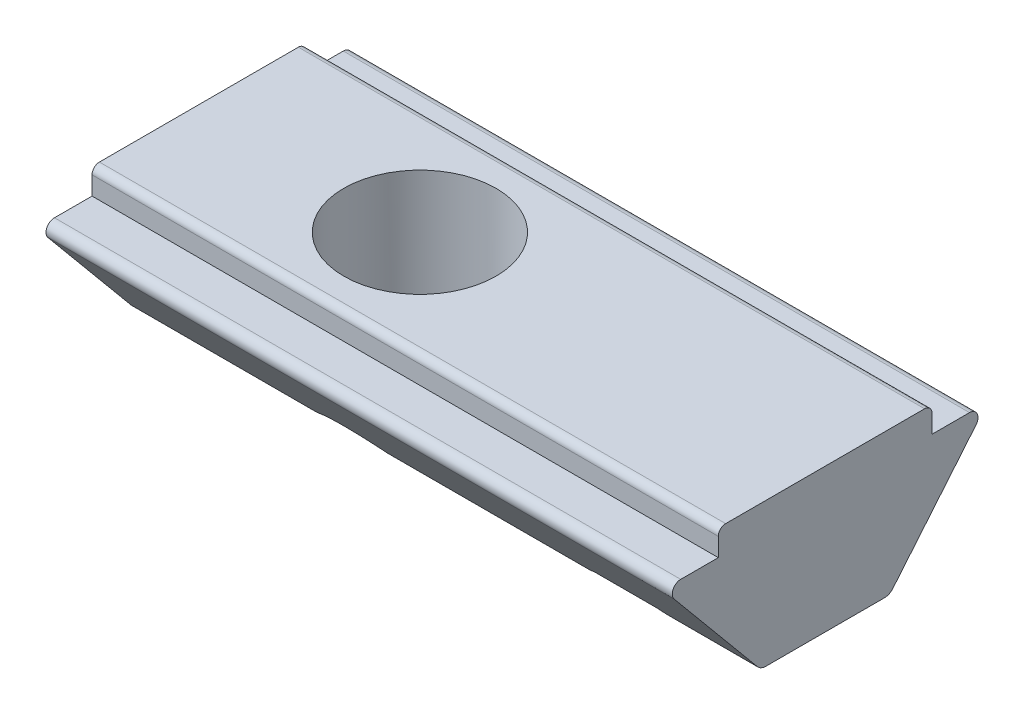
SolidWorks part; units mm, degrees
ref_plane "Front Plane" through (0, 0, 0) normal (0, 0, 1) x (1, 0, 0)
ref_plane "Top Plane" through (0, 0, 0) normal (0, 1, 0) x (1, 0, 0)
ref_plane "Right Plane" through (0, 0, 0) normal (1, 0, 0) x (0, 0, -1)
ref_plane "Plane1" through (-6, 0, 0) normal (1, 0, 0) x (0, 0, -1)
ref_plane "Plane2" through (7.5, 0, 0) normal (1, 0, 0) x (0, 0, -1)
ref_plane "Plane3" through (-3.1, 0, 0) normal (1, 0, 0) x (0, 0, -1)
sketch "Axis_Line_X" plane through (0, 0, 0) normal (0, 1, 0) x (1, 0, 0)
  line L0 (0, 0) -> (50, 0)
  dimension "FIX_2" = 50
sketch "Axis_Line_Z" plane through (0, 0, 0) normal (0, 1, 0) x (1, 0, 0)
  line L0 (0, 0) -> (0, -50)
  dimension "FIX_3" = 50
sketch "Sketch1" plane through (-6, 0, 0) normal (1, 0, 0) x (0, 0, -1)
  line L0 (2.9, 0) -> (-2.9, 0)
  line L1 (-2.9, 0) -> (-2.9, -0.7)
  line L2 (-2.9, -0.7) -> (-3.92, -0.7)
  line L3 (4.15, 0) -> (4.15, -3.9) construction
  line L4 (-4.0969, -1.077) -> (-1.75, -3.9)
  line L5 (-1.75, -3.9) -> (1.75, -3.9)
  line L6 (1.75, -3.9) -> (4.0969, -1.077)
  line L7 (-4.15, 0) -> (-4.15, -3.9) construction
  line L8 (3.92, -0.7) -> (2.9, -0.7)
  line L9 (2.9, -0.7) -> (2.9, 0)
  line L10 (0, 0) -> (0, -3.9) construction
  arc A2 (-4.0969, -1.077) -> (-3.92, -0.7) centre (-3.92, -0.93) cw
  arc A3 (4.0969, -1.077) -> (3.92, -0.7) centre (3.92, -0.93) ccw
  point P18 (-1.75, -3.9)
  point P21 (1.75, -3.9)
  dimension "FIX_6" = 0.23
  dimension "FIX_1" = 8.3
  dimension "FIX_3" = 5.8
  dimension "FIX_2" = 3.9
  dimension "FIX_5" = 3.2
  dimension "FIX_4" = 3.5
extrude "Boss-Extrude1" add sketch "Sketch1" along normal blind 17
fillet "Fillet1" radius 0.3 2 edges at (2.5, -3.9, 1.75) (2.5, -3.9, -1.75)
fillet "Fillet2" radius 0.2 2 edges at (2.5, 0, 2.9) (2.5, 0, -2.9)
sketch "Sketch2" plane through (7.5, 0, 0) normal (1, 0, 0) x (0, 0, -1)
  line L0 (0, 1.6655) -> (0, -9.505) construction
  line L2 (0, -3.7) -> (2.1, -3.7)
  line L3 (0, -3.7) -> (0, -3.9)
  line L4 (0, -3.9) -> (2.1, -3.9)
  line L5 (2.1, -3.7) -> (2.1, -3.9)
  dimension "FIX_12" = 0.2
  dimension "FIX_11" = 2.1
  dimension "FIX_10" = 3.9
revolve "Cut-Revolve1" cut sketch "Sketch2" angle 360 about L0
sketch "Sketch3" plane through (7.5, 0, 0) normal (1, 0, 0) x (0, 0, -1)
  line L0 (0, 0) -> (0, -4.7) construction
  line L1 (1.7321, -3.7) -> (0, -3.7) construction
  line L2 (1.7321, -4.7) -> (0, -4.7) construction
  line L3 (1.7321, -3.7) -> (0, -3.7)
  line L4 (0, -3.7) -> (0, -4.7)
  arc A0 (0, -4.7) -> (1.7321, -3.7) centre (0, -2.7) ccw
  dimension "FIX_16" = 4
  dimension "FIX_14" = 4.7
  dimension "FIX_15" = 3.7
revolve "Revolve1" add sketch "Sketch3" angle 360 about L0
hole_wizard "Tapped Hole1" positions "Sketch5" profile "Sketch4" tap size "M5x0.8" standard "JIS" end condition through all
sketch "Sketch5" plane through (0, 0, 0) normal (0, 1, 0) x (1, 0, 0)
  point P0 (0, 0)
sketch "Sketch4" plane through (0, 0, 0) normal (1, 0, 0) x (0, 0, 1)
  line L0 (0, 0) -> (0, 4.7)
  line L1 (0, 4.7) -> (2.067, 4.7)
  line L2 (2.067, 4.7) -> (2.067, 0)
  line L5 (2.067, 0) -> (0, 0)
  line L11 (0, 0) -> (0, 4.7) construction
  dimension "Thru Tap Drill Dia." = 4.134
  dimension "Thru Tap Drill Depth" = 4.7
cosmetic thread "Thread1" parameters "NFIX_1"=5
sketch "Sketch6" [suppressed] plane through (-3.1, 0, 0) normal (1, 0, 0) x (0, 0, -1)
  line L0 (3.4, -0.6) -> (3.4, -0.7) construction
  line L1 (3.4, -0.6) -> (3.4, -0.7)
  line L2 (3.4, -0.7) -> (3.5, -0.7)
  arc A0 (3.5, -0.7) -> (3.4, -0.6) centre (3.4, -0.7) ccw
  dimension "FIX_20" = 0.1
  dimension "FIX_19" = 0.7
  dimension "FIX_18" = 3.4
revolve "Revolve2" [suppressed] add sketch "Sketch6" angle 360 about L0
pattern_linear "LPattern1" [suppressed]
equation "\"SHNTP5\" = if ( \"L1\" = 6 , \"suppressed\" , \"unsuppressed\" )"
